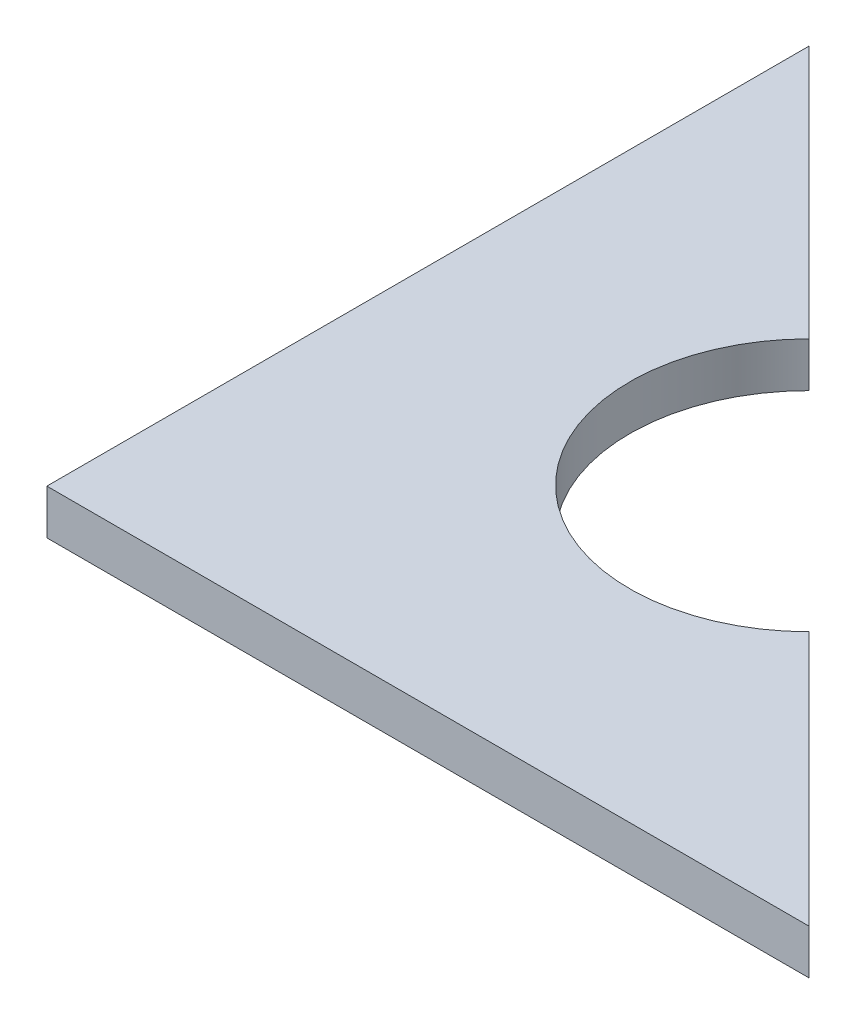
SolidWorks part; units mm, degrees
ref_plane "Face" through (0, 0, 0) normal (0, 0, 1) x (1, 0, 0)
ref_plane "Dessus" through (0, 0, 0) normal (0, 1, 0) x (1, 0, 0)
ref_plane "Droite" through (0, 0, 0) normal (1, 0, 0) x (0, 0, -1)
sketch "Esquisse1" plane through (0, 0, 0) normal (0, 1, 0) x (1, 0, 0)
  line L0 (-14.2203, 14.2203) -> (-42.5, 42.5)
  line L1 (42.5, -42.5) -> (-42.5, -42.5)
  line L2 (42.5, -42.5) -> (42.5, 42.5) construction
  line L3 (42.5, 42.5) -> (-42.5, 42.5) construction
  line L4 (-42.5, -42.5) -> (-42.5, 42.5)
  line L5 (42.5, -42.5) -> (-42.5, 42.5) construction
  line L6 (42.5, 42.5) -> (-42.5, -42.5) construction
  line L7 (-42.5, 42.5) -> (-42.2614, 42.1552)
  line L8 (14.064, -14.064) -> (42.5, -42.5)
  circle A0 centre (-0.0782, 0.0782) radius 20 construction
  arc A1 (14.064, -14.064) -> (-14.2203, 14.2203) centre (-0.0782, 0.0782) cw
  point P0 (0, 0)
  dimension "D1" = 85
  dimension "D3" = 40
  dimension "D2" = 85
extrude "Boss.-Extru.1" add sketch "Esquisse1" along normal blind 5
